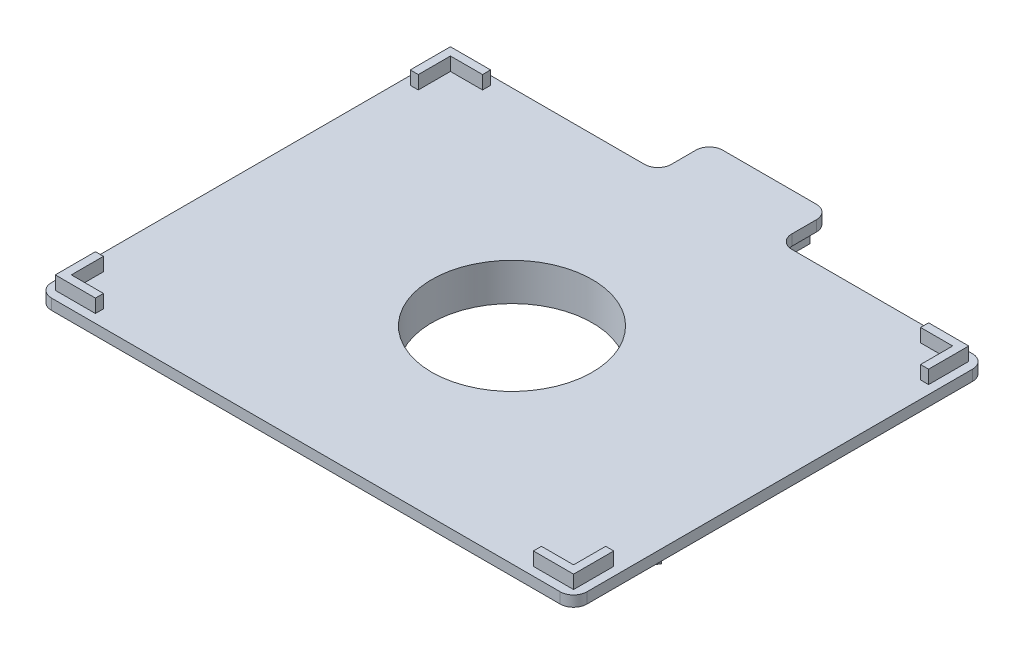
SolidWorks part; units mm, degrees
ref_plane "Front" through (0, 0, 0) normal (0, 0, 1) x (1, 0, 0)
ref_plane "Top" through (0, 0, 0) normal (0, 1, 0) x (1, 0, 0)
ref_plane "Right" through (0, 0, 0) normal (1, 0, 0) x (0, 0, -1)
sketch "Sketch1" plane through (0, 0, 0) normal (0, 1, 0) x (1, 0, 0)
  line L0 (11.29, 86.1984) -> (-11.29, 86.1984) construction
  line L1 (-15.08, 76.1984) -> (-7.5, 76.1984)
  line L2 (-15.08, 76.1984) -> (-15.08, 96.1984)
  line L3 (-15.08, 96.1984) -> (-7.5, 96.1984)
  line L4 (-7.5, 76.1984) -> (-7.5, 96.1984)
  line L5 (-15.08, 76.1984) -> (-7.5, 96.1984) construction
  line L6 (-15.08, 96.1984) -> (-7.5, 76.1984) construction
  line L7 (7.5, 76.1984) -> (15.08, 76.1984)
  line L8 (7.5, 76.1984) -> (7.5, 96.1984)
  line L9 (7.5, 96.1984) -> (15.08, 96.1984)
  line L10 (15.08, 76.1984) -> (15.08, 96.1984)
  line L11 (7.5, 76.1984) -> (15.08, 96.1984) construction
  line L12 (7.5, 96.1984) -> (15.08, 76.1984) construction
  line L13 (0, -55) -> (0, 55) construction
  line L14 (62.2397, -44.5944) -> (79.5603, -54.5944)
  line L15 (62.2397, -44.5944) -> (58.4497, -51.1589)
  line L16 (58.4497, -51.1589) -> (75.7703, -61.1589)
  line L17 (79.5603, -54.5944) -> (75.7703, -61.1589)
  line L18 (69.005, -52.8766) -> (80.295, -33.3218) construction
  line L19 (73.5297, -25.0395) -> (90.8503, -35.0395)
  line L20 (73.5297, -25.0395) -> (69.7397, -31.604)
  line L21 (69.7397, -31.604) -> (87.0603, -41.604)
  line L22 (90.8503, -35.0395) -> (87.0603, -41.604)
  line L23 (-69.7397, -31.604) -> (-87.0603, -41.604)
  line L24 (-69.7397, -31.604) -> (-73.5297, -25.0395)
  line L25 (-73.5297, -25.0395) -> (-90.8503, -35.0395)
  line L26 (-87.0603, -41.604) -> (-90.8503, -35.0395)
  line L27 (-80.295, -33.3218) -> (-69.005, -52.8766) construction
  line L28 (-58.4497, -51.1589) -> (-75.7703, -61.1589)
  line L29 (-58.4497, -51.1589) -> (-62.2397, -44.5944)
  line L30 (-62.2397, -44.5944) -> (-79.5603, -54.5944)
  line L31 (-75.7703, -61.1589) -> (-79.5603, -54.5944)
  line L32 (-7.5, 76.1984) -> (-23.8103, 47.9482)
  line L33 (-62.2397, -44.5944) -> (-29.6192, -44.5944)
  line L34 (69.7397, -31.604) -> (53.4295, -3.3538)
  line L35 (-53.4295, -3.3538) -> (-69.7397, -31.604)
  line L36 (29.6192, -44.5944) -> (62.2397, -44.5944)
  line L37 (23.8103, 47.9482) -> (7.5, 76.1984)
  arc A1 (15.08, 76.1984) -> (73.5297, -25.0395) centre (-121.3385, -70.0548) cw
  arc A2 (23.8103, 47.9482) -> (-23.8103, 47.9482) centre (0, 66.1984) cw
  arc A3 (-15.08, 76.1984) -> (-73.5297, -25.0395) centre (121.3385, -70.0548) ccw
  arc A4 (29.6192, -44.5944) -> (53.4295, -3.3538) centre (57.3295, -33.0992) cw
  arc A5 (-58.4497, -51.1589) -> (58.4497, -51.1589) centre (0, 140.1096) ccw
  arc A6 (-53.4295, -3.3538) -> (-29.6192, -44.5944) centre (-57.3295, -33.0992) cw
  circle A7 centre (0, 0) radius 30
  point P0 (-11.29, 86.1984)
  point P5 (11.29, 86.1984)
  point P12 (0, 86.1984)
  point P37 (0, 0)
  point P40 (-74.65, -43.0992)
  point P51 (0, 0)
  point P55 (0, 0)
  dimension "D5" = 60
  dimension "D6" = 200
  dimension "D7" = 30
  dimension "D9" = 10
  dimension "D1" = 7.58
  dimension "D3" = 149.3
  dimension "D4" = 15
  dimension "D8" = 20
  dimension "D2" = 3
extrude "Boss-Extrude1" add sketch "Sketch1" along normal blind 10
sketch "Sketch2" plane through (15.08, 0, 0) normal (1, 0, 0) x (0, 0, -1)
  line L2 (76.1984, 10) -> (76.1984, 0) construction
  line L3 (76.1984, 0) -> (96.1984, 0) construction
  circle A0 centre (86.1984, 3) radius 1.5
  dimension "D1" = 3
  dimension "D2" = 10
  dimension "D3" = 3
extrude "Cut-Extrude1" cut sketch "Sketch2" against normal through all both and the other way through all
pattern_circular "CirPattern1" count 3 over 240 about axis through (0, 10, 0) along (0, -1, 0) of "Cut-Extrude1"
fillet "Fillet1" radius 7 18 edges at (29.6192, 5, 44.5944) (53.4295, 5, 3.3538) (-23.8103, 5, -47.9482) (23.8103, 5, -47.9482) (-29.6192, 5, 44.5944) (-53.4295, 5, 3.3538) (-58.4497, 5, 51.1589) (58.4497, 5, 51.1589) (73.5297, 5, 25.0395) (-73.5297, 5, 25.0395) (-15.08, 5, -76.1984) (15.08, 5, -76.1984) (-62.2397, 5, 44.5944) (-69.7397, 5, 31.604) (62.2397, 5, 44.5944) (69.7397, 5, 31.604) (-7.5, 5, -76.1984) (7.5, 5, -76.1984)
sketch "Sketch4" plane through (0, 10, 0) normal (0, 1, 0) x (1, 0, 0)
  line L0 (0, -5.5) -> (0, 5.5) construction
  line L1 (-95, -77) -> (95, -77)
  line L2 (-100, -72) -> (-100, 72)
  line L3 (-95, 77) -> (95, 77)
  line L4 (100, -72) -> (100, 72)
  line L5 (-100, -77) -> (100, 77) construction
  line L6 (-100, 77) -> (100, -77) construction
  line L7 (-22.5, 77) -> (22.5, 77)
  line L8 (-22.5, 77) -> (-22.5, 91.1984)
  line L9 (-17.5, 96.1984) -> (17.5, 96.1984)
  line L10 (22.5, 77) -> (22.5, 91.1984)
  line L11 (-22.5, 77) -> (22.5, 96.1984) construction
  line L12 (-22.5, 96.1984) -> (22.5, 77) construction
  line L13 (7.5, 96.1984) -> (15.08, 96.1984) construction
  arc A1 (95, -77) -> (100, -72) centre (95, -72) ccw
  arc A2 (-95, -77) -> (-100, -72) centre (-95, -72) cw
  arc A3 (-100, 72) -> (-95, 77) centre (-95, 72) cw
  arc A4 (95, 77) -> (100, 72) centre (95, 72) cw
  circle A5 centre (0, 0) radius 30
  arc A6 (-22.5, 91.1984) -> (-17.5, 96.1984) centre (-17.5, 91.1984) cw
  arc A7 (17.5, 96.1984) -> (22.5, 91.1984) centre (17.5, 91.1984) cw
  point P0 (0, 0)
  point P6 (0, 86.5992)
  circle M20 centre (0, 0) radius 30
  line M21 (-34.773, -44.5944) -> (-60.3641, -44.5944)
  arc M22 (-60.3641, -44.5944) -> (-63.8641, -45.5322) centre (-60.3641, -51.5944) ccw
  line M23 (-63.8641, -45.5322) -> (-79.5603, -54.5944)
  line M24 (-79.5603, -54.5944) -> (-75.7703, -61.1589)
  line M25 (-75.7703, -61.1589) -> (-61.0583, -52.6649)
  arc M26 (-61.0583, -52.6649) -> (-55.6119, -52.0032) centre (-57.5583, -58.7271) cw
  arc M27 (-55.6119, -52.0032) -> (55.6119, -52.0032) centre (0, 140.1096) ccw
  arc M28 (55.6119, -52.0032) -> (61.0583, -52.6649) centre (57.5583, -58.7271) cw
  line M29 (61.0583, -52.6649) -> (75.7703, -61.1589)
  line M30 (75.7703, -61.1589) -> (79.5603, -54.5944)
  line M31 (79.5603, -54.5944) -> (63.8641, -45.5322)
  arc M32 (63.8641, -45.5322) -> (60.3641, -44.5944) centre (60.3641, -51.5944) ccw
  line M33 (60.3641, -44.5944) -> (34.773, -44.5944)
  arc M34 (34.773, -44.5944) -> (27.908, -38.9625) centre (34.773, -37.5944) cw
  arc M35 (27.908, -38.9625) -> (47.6965, -4.6878) centre (57.3295, -33.0992) cw
  arc M36 (47.6965, -4.6878) -> (56.0064, -7.8171) centre (49.9442, -11.3171) cw
  line M37 (56.0064, -7.8171) -> (68.8019, -29.9797)
  arc M38 (68.8019, -29.9797) -> (71.3641, -32.5418) centre (74.8641, -26.4797) ccw
  line M39 (71.3641, -32.5418) -> (87.0603, -41.604)
  line M40 (87.0603, -41.604) -> (90.8503, -35.0395)
  line M41 (90.8503, -35.0395) -> (76.1383, -26.5456)
  arc M42 (76.1383, -26.5456) -> (72.842, -22.1598) centre (79.6383, -20.4834) cw
  arc M43 (72.842, -22.1598) -> (17.2301, 74.1629) centre (-121.3385, -70.0548) ccw
  arc M44 (17.2301, 74.1629) -> (15.08, 79.2105) centre (22.08, 79.2105) cw
  line M45 (15.08, 79.2105) -> (15.08, 96.1984)
  line M46 (15.08, 96.1984) -> (7.5, 96.1984)
  line M47 (7.5, 96.1984) -> (7.5, 78.074)
  arc M48 (7.5, 78.074) -> (8.4378, 74.574) centre (14.5, 78.074) ccw
  line M49 (8.4378, 74.574) -> (21.2334, 52.4115)
  arc M50 (21.2334, 52.4115) -> (19.7885, 43.6503) centre (15.1712, 48.9115) cw
  arc M51 (19.7885, 43.6503) -> (-19.7885, 43.6503) centre (0, 66.1984) cw
  arc M52 (-19.7885, 43.6503) -> (-21.2334, 52.4115) centre (-15.1712, 48.9115) cw
  line M53 (-21.2334, 52.4115) -> (-8.4378, 74.574)
  arc M54 (-8.4378, 74.574) -> (-7.5, 78.074) centre (-14.5, 78.074) ccw
  line M55 (-7.5, 78.074) -> (-7.5, 96.1984)
  line M56 (-7.5, 96.1984) -> (-15.08, 96.1984)
  line M57 (-15.08, 96.1984) -> (-15.08, 79.2105)
  arc M58 (-15.08, 79.2105) -> (-17.2301, 74.1629) centre (-22.08, 79.2105) cw
  arc M59 (-17.2301, 74.1629) -> (-72.842, -22.1598) centre (121.3385, -70.0548) ccw
  arc M60 (-72.842, -22.1598) -> (-76.1383, -26.5456) centre (-79.6383, -20.4834) cw
  line M61 (-76.1383, -26.5456) -> (-90.8503, -35.0395)
  line M62 (-90.8503, -35.0395) -> (-87.0603, -41.604)
  line M63 (-87.0603, -41.604) -> (-71.3641, -32.5418)
  arc M64 (-71.3641, -32.5418) -> (-68.8019, -29.9797) centre (-74.8641, -26.4797) ccw
  line M65 (-68.8019, -29.9797) -> (-56.0064, -7.8171)
  arc M66 (-56.0064, -7.8171) -> (-47.6965, -4.6878) centre (-49.9442, -11.3171) cw
  arc M67 (-47.6965, -4.6878) -> (-27.908, -38.9625) centre (-57.3295, -33.0992) cw
  arc M68 (-27.908, -38.9625) -> (-34.773, -44.5944) centre (-34.773, -37.5944) cw
  dimension "D3" = 5
  dimension "D4" = 5
  dimension "D6" = 60
  dimension "D1" = 200
  dimension "D2" = 154
  dimension "D5" = 45
extrude "Boss-Extrude4" add sketch "Sketch4" along normal blind 4 contours A4 L3 A3 L2 A2 L1 A1 L4 M43 M42 M41 M40 M39 M38 M37 M36 M35 M34 M33 M32 M31 M30 M29 M28 M27 M26 M25 M24 M23 M22 M21 M68 M67 M66 M65 M64 M63 M62 M61 M60 M59 | L9 L3 M55 M54 M53 M49 M48 M47 | L9 L8 M59 M58 M57 | L3 M49 M43 M44 M45 M46 M47 M48 | L10 L9 M43 M45 M44 | L3 M59 M60 M61 M62 M63 M64 M65 M66 M67 M68 M21 M22 M23 M24 M25 M26 M27 M28 M29 M30 M31 M32 M33 M34 M35 M36 M37 M38 M39 M40 M41 M42 M43 M49 M50 M51 M52 M53 M20 | L3 M59 M53 M54 M55 M56 M57 M58 | A5
sketch "Sketch5" plane through (0, 14, 0) normal (0, 1, 0) x (1, 0, 0)
  line L0 (-96.8, 73.8) -> (-81.8, 73.8)
  line L2 (-93.8, 58.8) -> (-93.8, 70.8)
  line L3 (-93.8, 70.8) -> (-81.8, 70.8)
  line L5 (-5.5, 0) -> (5.5, 0) construction
  line L6 (0, -5.5) -> (0, 5.5) construction
  line L9 (-96.8, 58.8) -> (-96.8, 73.8)
  line L10 (-81.8, 73.8) -> (-81.8, 70.8)
  line L11 (-93.8, 58.8) -> (-96.8, 58.8)
  line L12 (-93.8, 70.8) -> (93.7, 70.8) construction
  line L13 (-96.8, 73.8) -> (96.7, 73.8) construction
  line L14 (-93.8, -70.75) -> (-93.8, 70.8) construction
  line L15 (-96.8, -73.75) -> (-96.8, 73.8) construction
  line L16 (93.7, -70.75) -> (93.7, 70.8) construction
  line L17 (96.7, -73.75) -> (96.7, 73.8) construction
  line L18 (-93.8, -70.75) -> (93.7, -70.75) construction
  line L19 (-96.8, -73.75) -> (96.7, -73.75) construction
  line L20 (93.8, 70.8) -> (81.8, 70.8)
  line L21 (81.8, 73.8) -> (81.8, 70.8)
  line L22 (96.8, 73.8) -> (81.8, 73.8)
  line L23 (93.8, 58.8) -> (96.8, 58.8)
  line L24 (96.8, 58.8) -> (96.8, 73.8)
  line L25 (93.8, 58.8) -> (93.8, 70.8)
  line L26 (93.8, -58.8) -> (93.8, -70.8)
  line L27 (93.8, -58.8) -> (96.8, -58.8)
  line L28 (96.8, -58.8) -> (96.8, -73.8)
  line L29 (96.8, -73.8) -> (81.8, -73.8)
  line L30 (81.8, -73.8) -> (81.8, -70.8)
  line L31 (93.8, -70.8) -> (81.8, -70.8)
  line L32 (-93.8, -58.8) -> (-96.8, -58.8)
  line L33 (-96.8, -58.8) -> (-96.8, -73.8)
  line L34 (-96.8, -73.8) -> (-81.8, -73.8)
  line L35 (-81.8, -73.8) -> (-81.8, -70.8)
  line L36 (-93.8, -70.8) -> (-81.8, -70.8)
  line L37 (-93.8, -58.8) -> (-93.8, -70.8)
  point P0 (0, 0)
  dimension "D1" = 96.8
  dimension "D2" = 73.8
  dimension "D4" = 15
  dimension "D5" = 15
  dimension "D3" = 3
extrude "Boss-Extrude5" add sketch "Sketch5" along normal blind 5
fillet "Fillet4" radius 5 2 edges at (-22.5, 12, -77) (22.5, 12, -77)
